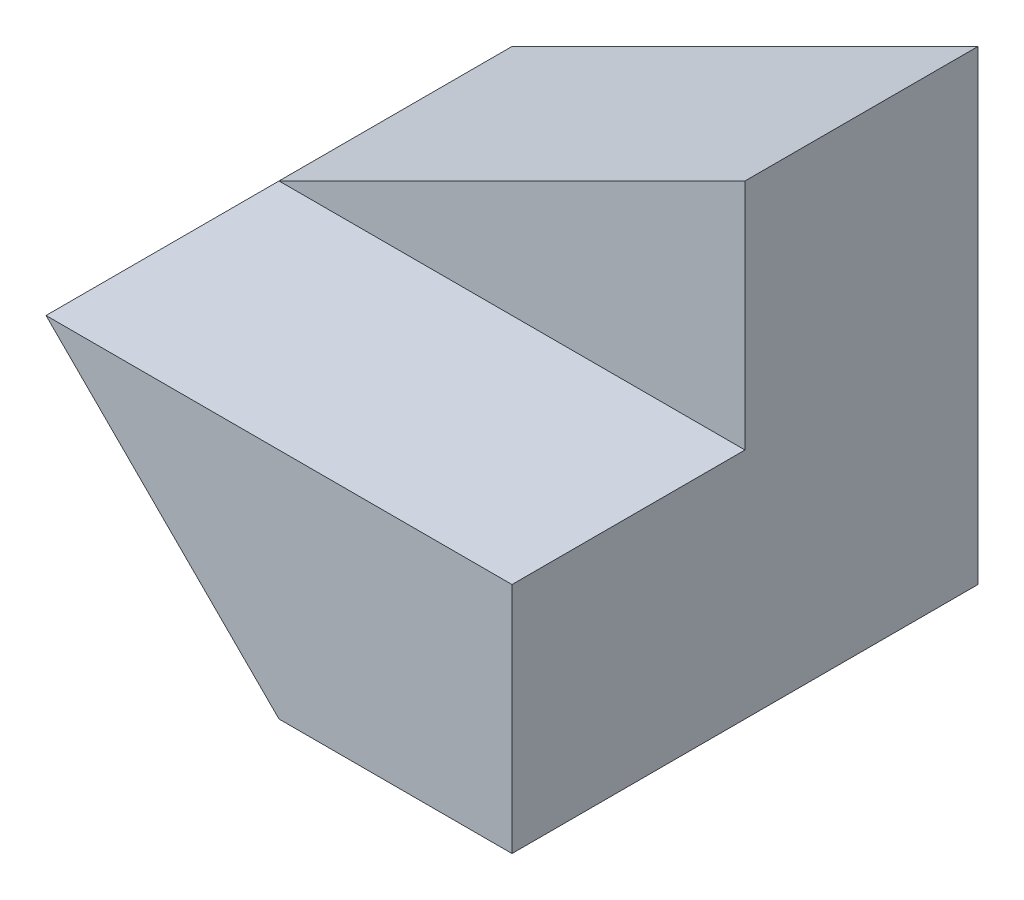
SolidWorks part; units mm, degrees
ref_plane "Front Plane" through (0, 0, 0) normal (0, 0, 1) x (1, 0, 0)
ref_plane "Top Plane" through (0, 0, 0) normal (0, 1, 0) x (1, 0, 0)
ref_plane "Right Plane" through (0, 0, 0) normal (1, 0, 0) x (0, 0, -1)
sketch "Sketch1" plane through (0, 0, 0) normal (0, 0, 1) x (1, 0, 0)
  line L1 (0, 0) -> (40, 0)
  line L2 (0, 0) -> (0, 40)
  line L3 (0, 40) -> (40, 40)
  line L4 (40, 0) -> (40, 40)
  dimension "D1" = 40
  dimension "D2" = 40
extrude "Boss-Extrude1" add sketch "Sketch1" along normal blind 40
sketch "Sketch2" plane through (0, 0, 40) normal (0, 0, 1) x (1, 0, 0)
  line L0 (40, 40) -> (0, 40)
  line L1 (0, 40) -> (0, 20)
  line L2 (0, 40) -> (0, 0) construction
  line L3 (0, 20) -> (40, 40)
extrude "Cut-Extrude1" cut sketch "Sketch2" against normal blind 40
sketch "Sketch3" plane through (40, 0, 0) normal (1, 0, 0) x (0, 0, -1)
  line L1 (-40, 40) -> (-20, 40)
  line L2 (-40, 40) -> (-40, 20)
  line L3 (-40, 20) -> (-20, 20)
  line L4 (-20, 40) -> (-20, 20)
  dimension "D1" = 20
  dimension "D2" = 20
extrude "Cut-Extrude2" cut sketch "Sketch3" against normal blind 40
sketch "Sketch4" plane through (0, 0, 40) normal (0, 0, 1) x (1, 0, 0)
  line L0 (0, 20) -> (20, 0)
  line L1 (0, 0) -> (40, 0) construction
  line L2 (20, 0) -> (0, 0)
  line L3 (0, 0) -> (0, 20)
extrude "Cut-Extrude4" cut sketch "Sketch4" against normal blind 20
